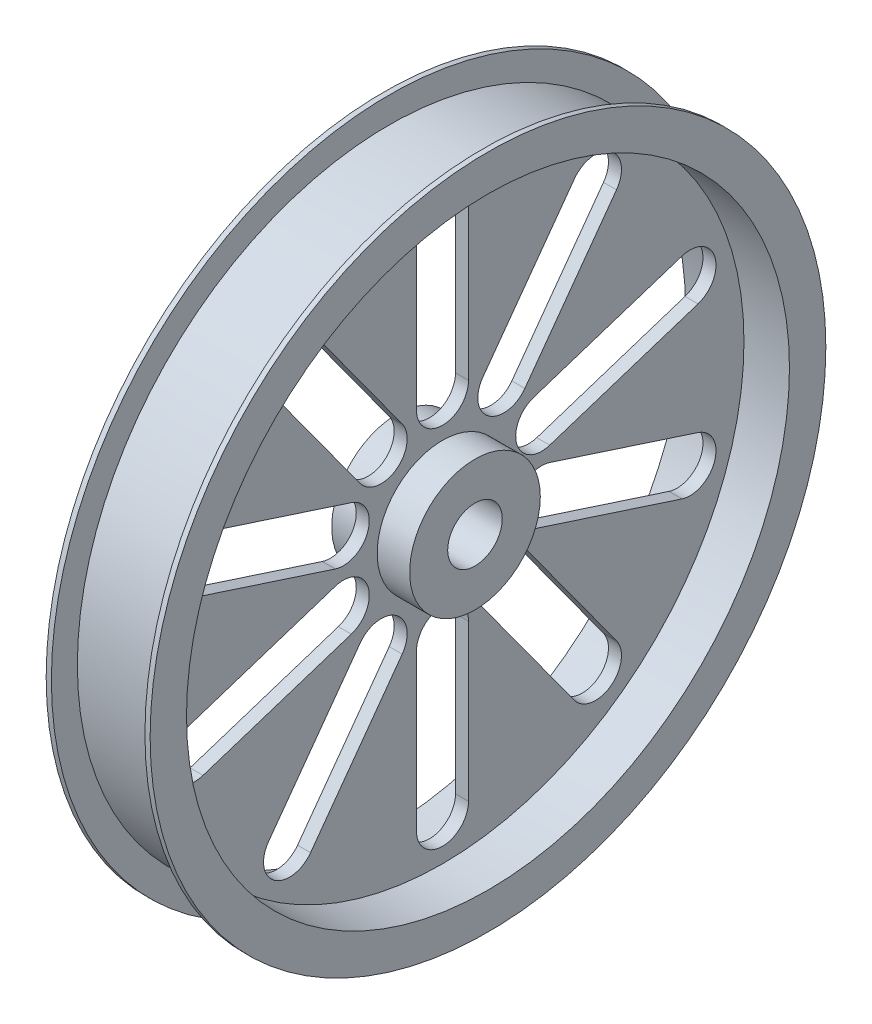
SolidWorks part; units mm, degrees
material "1060 Alloy"
ref_plane "Front Plane" through (0, 0, 0) normal (0, 0, 1) x (1, 0, 0)
ref_plane "Top Plane" through (0, 0, 0) normal (0, 1, 0) x (1, 0, 0)
ref_plane "Right Plane" through (0, 0, 0) normal (1, 0, 0) x (0, 0, -1)
other "Configuration Table"
sketch "Sketch2" plane through (0, 0, 0) normal (0, 0, 1) x (1, 0, 0)
  line L0 (0, 0) -> (0, -81.8247) construction
  line L1 (217.8737, 0) -> (-217.8737, 0) construction
  line L3 (22.86, 152.4) -> (-22.86, 152.4)
  line L4 (-22.86, 152.4) -> (-22.86, 165.1)
  line L5 (-22.86, 165.1) -> (-25.4, 165.1)
  line L6 (-25.4, 165.1) -> (-25.4, 147.32)
  line L7 (-25.4, 147.32) -> (-3.175, 147.32)
  line L8 (-3.175, 147.32) -> (-3.175, 31.9233)
  line L9 (-3.175, 31.9233) -> (-19.05, 31.9233)
  line L10 (-19.05, 31.9233) -> (-19.05, 0)
  line L11 (-19.05, 0) -> (19.05, 0)
  line L12 (19.05, 31.9233) -> (19.05, 0)
  line L13 (3.175, 31.9233) -> (19.05, 31.9233)
  line L14 (3.175, 147.32) -> (3.175, 31.9233)
  line L15 (25.4, 147.32) -> (3.175, 147.32)
  line L16 (25.4, 165.1) -> (25.4, 147.32)
  line L17 (22.86, 165.1) -> (25.4, 165.1)
  line L18 (22.86, 152.4) -> (22.86, 165.1)
  dimension "D1" = 330.2
  dimension "D2" = 50.8
  dimension "D3" = 38.1
  dimension "D4" = 6.35
  dimension "D5" = 12.7
  dimension "D6" = 17.78
  dimension "D7" = 2.54
  dimension "D8" = 31.9233
revolve "Revolve2" add sketch "Sketch2" angle 360 about L1
sketch "Sketch3" plane through (-19.05, 0, 0) normal (-1, 0, 0) x (0, 0, 1)
  circle A0 centre (0, 0) radius 13.335
  dimension "D1" = 26.67
extrude "Cut-Extrude1" cut sketch "Sketch3" against normal through all both
sketch "Sketch4" plane through (-3.175, 0, 0) normal (-1, 0, 0) x (0, 0, 1)
  line L0 (0, 31.9233) -> (0, 147.32) construction
  line L1 (0, 127.1733) -> (0, 50.9733) construction
  line L2 (12.7, 127.1733) -> (12.7, 50.9733)
  line L3 (-12.7, 127.1733) -> (-12.7, 50.9733)
  line L4 (64.4761, 110.3503) -> (19.6869, 48.7032)
  line L5 (85.0251, 95.4205) -> (40.2359, 33.7734)
  line L6 (74.7506, 102.8854) -> (29.9614, 41.2383) construction
  line L7 (117.0245, 51.3771) -> (44.554, 27.83)
  line L8 (124.8736, 27.2203) -> (52.403, 3.6732)
  line L9 (120.949, 39.2987) -> (48.4785, 15.7516) construction
  line L10 (124.8736, -27.2203) -> (52.403, -3.6732)
  line L11 (117.0245, -51.3771) -> (44.554, -27.83)
  line L12 (120.949, -39.2987) -> (48.4785, -15.7516) construction
  line L13 (85.0251, -95.4205) -> (40.2359, -33.7734)
  line L14 (64.4761, -110.3503) -> (19.6869, -48.7032)
  line L15 (74.7506, -102.8854) -> (29.9614, -41.2383) construction
  line L16 (12.7, -127.1733) -> (12.7, -50.9733)
  line L17 (-12.7, -127.1733) -> (-12.7, -50.9733)
  line L18 (0, -127.1733) -> (0, -50.9733) construction
  line L19 (-64.4761, -110.3503) -> (-19.6869, -48.7032)
  line L20 (-85.0251, -95.4205) -> (-40.2359, -33.7734)
  line L21 (-74.7506, -102.8854) -> (-29.9614, -41.2383) construction
  line L22 (-117.0245, -51.3771) -> (-44.554, -27.83)
  line L23 (-124.8736, -27.2203) -> (-52.403, -3.6732)
  line L24 (-120.949, -39.2987) -> (-48.4785, -15.7516) construction
  line L25 (-124.8736, 27.2203) -> (-52.403, 3.6732)
  line L26 (-117.0245, 51.3771) -> (-44.554, 27.83)
  line L27 (-120.949, 39.2987) -> (-48.4785, 15.7516) construction
  line L28 (-85.0251, 95.4205) -> (-40.2359, 33.7734)
  line L29 (-64.4761, 110.3503) -> (-19.6869, 48.7032)
  line L30 (-74.7506, 102.8854) -> (-29.9614, 41.2383) construction
  circle A0 centre (0, 0) radius 31.9233 construction
  circle A1 centre (0, 0) radius 31.9233 construction
  circle A2 centre (0, 0) radius 147.32 construction
  arc A3 (12.7, 127.1733) -> (-12.7, 127.1733) centre (0, 127.1733) ccw
  arc A4 (-12.7, 50.9733) -> (12.7, 50.9733) centre (0, 50.9733) ccw
  arc A5 (85.0251, 95.4205) -> (64.4761, 110.3503) centre (74.7506, 102.8854) ccw
  arc A6 (19.6869, 48.7032) -> (40.2359, 33.7734) centre (29.9614, 41.2383) ccw
  arc A7 (124.8736, 27.2203) -> (117.0245, 51.3771) centre (120.949, 39.2987) ccw
  arc A8 (44.554, 27.83) -> (52.403, 3.6732) centre (48.4785, 15.7516) ccw
  arc A9 (117.0245, -51.3771) -> (124.8736, -27.2203) centre (120.949, -39.2987) ccw
  arc A10 (52.403, -3.6732) -> (44.554, -27.83) centre (48.4785, -15.7516) ccw
  arc A11 (64.4761, -110.3503) -> (85.0251, -95.4205) centre (74.7506, -102.8854) ccw
  arc A12 (40.2359, -33.7734) -> (19.6869, -48.7032) centre (29.9614, -41.2383) ccw
  arc A13 (-12.7, -127.1733) -> (12.7, -127.1733) centre (0, -127.1733) ccw
  arc A14 (12.7, -50.9733) -> (-12.7, -50.9733) centre (0, -50.9733) ccw
  arc A15 (-85.0251, -95.4205) -> (-64.4761, -110.3503) centre (-74.7506, -102.8854) ccw
  arc A16 (-19.6869, -48.7032) -> (-40.2359, -33.7734) centre (-29.9614, -41.2383) ccw
  arc A17 (-124.8736, -27.2203) -> (-117.0245, -51.3771) centre (-120.949, -39.2987) ccw
  arc A18 (-44.554, -27.83) -> (-52.403, -3.6732) centre (-48.4785, -15.7516) ccw
  arc A19 (-117.0245, 51.3771) -> (-124.8736, 27.2203) centre (-120.949, 39.2987) ccw
  arc A20 (-52.403, 3.6732) -> (-44.554, 27.83) centre (-48.4785, 15.7516) ccw
  arc A21 (-64.4761, 110.3503) -> (-85.0251, 95.4205) centre (-74.7506, 102.8854) ccw
  arc A22 (-40.2359, 33.7734) -> (-19.6869, 48.7032) centre (-29.9614, 41.2383) ccw
  circle A23 centre (0, 0) radius 147.32
  circle A24 centre (0, 0) radius 31.9233
  point P11 (0, 89.0733)
  point P21 (52.356, 72.0618)
  point P28 (84.7138, 27.5252)
  point P35 (84.7138, -27.5252)
  point P42 (52.356, -72.0618)
  point P49 (0, -89.0733)
  point P56 (-52.356, -72.0618)
  point P63 (-84.7138, -27.5252)
  point P70 (-84.7138, 27.5252)
  point P77 (-52.356, 72.0618)
  point P82 (0, 0)
  dimension "D1" = 12.7
  dimension "D2" = 76.2
  dimension "D3" = 57.15
  dimension "D4" = 10
extrude "Cut-Extrude10" cut sketch "Sketch4" against normal through all both contours L26 A20 L25 A19 | L23 A18 L22 A17 | L20 A16 L19 A15 | L17 A14 L16 A13 | L14 A12 L13 A11 | L11 A10 L10 A9 | L8 A8 L7 A7 | L5 A6 L4 A5 | L3 A4 L2 A3 | L29 A22 L28 A21
equation "\"A\"= 3"
equation "\"B\"= 1"
